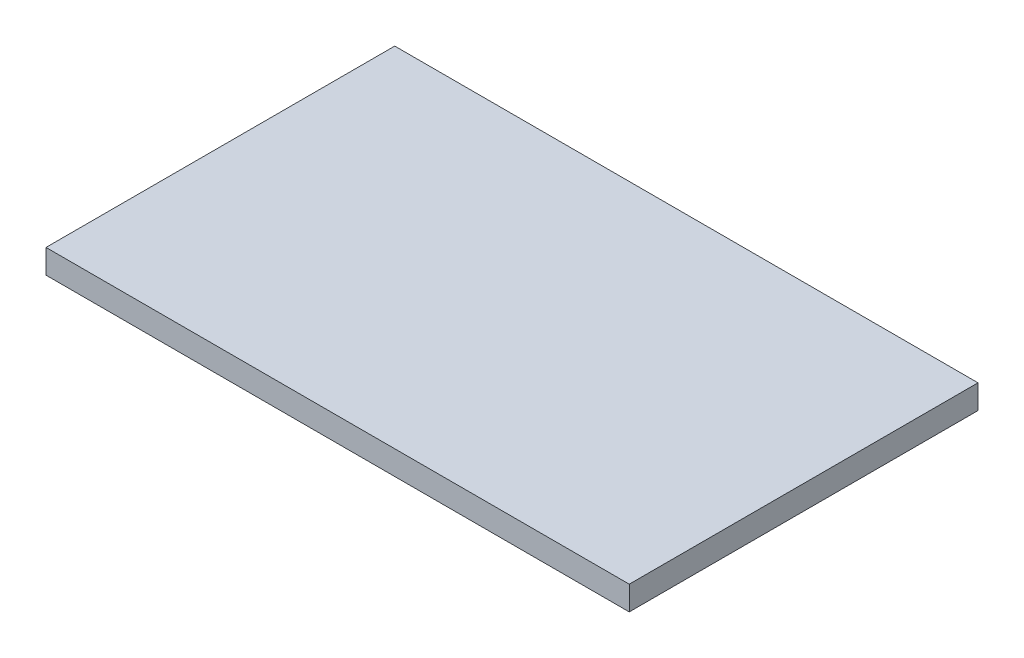
SolidWorks part; units mm, degrees
material "Acrylic (Medium-high impact)"
ref_plane "Front Plane" through (0, 0, 0) normal (0, 0, 1) x (1, 0, 0)
ref_plane "Top Plane" through (0, 0, 0) normal (0, 1, 0) x (1, 0, 0)
ref_plane "Right Plane" through (0, 0, 0) normal (1, 0, 0) x (0, 0, -1)
sketch "Sketch1" plane through (0, 0, 0) normal (0, 1, 0) x (1, 0, 0)
  line L1 (0, 0) -> (48.5, 0)
  line L2 (0, 0) -> (0, -29)
  line L3 (0, -29) -> (48.5, -29)
  line L4 (48.5, 0) -> (48.5, -29)
  dimension "D1" = 48.5
  dimension "D2" = 29
extrude "Boss-Extrude1" add sketch "Sketch1" along normal blind 2
